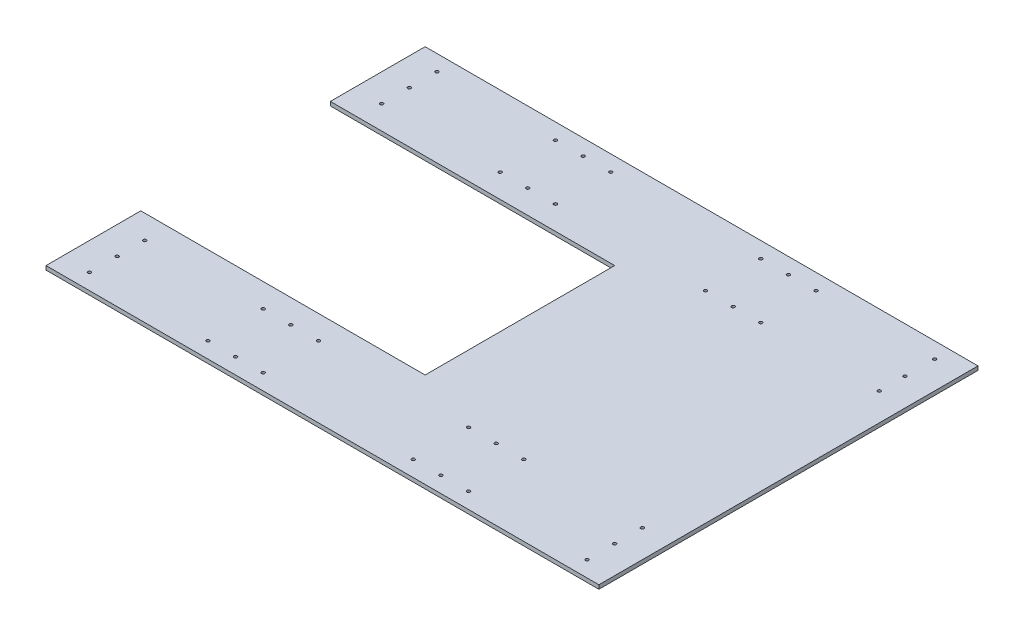
SolidWorks part; units mm, degrees
ref_plane "Front Plane" through (0, 0, 0) normal (0, 0, 1) x (1, 0, 0)
ref_plane "Top Plane" through (0, 0, 0) normal (0, 1, 0) x (1, 0, 0)
ref_plane "Right Plane" through (0, 0, 0) normal (1, 0, 0) x (0, 0, -1)
sketch "Sketch1" plane through (0, 0, 0) normal (0, 1, 0) x (1, 0, 0)
  line L1 (0, 0) -> (889, 0)
  line L2 (0, 0) -> (0, 609.6)
  line L3 (0, 609.6) -> (889, 609.6)
  line L4 (889, 0) -> (889, 609.6)
  dimension "D1" = 609.6
  dimension "D2" = 889
extrude "Boss-Extrude1" add sketch "Sketch1" along normal blind 6.35
sketch "Sketch2" plane through (0, 6.35, 0) normal (0, 1, 0) x (1, 0, 0)
  line L0 (0, 609.6) -> (0, 0) construction
  line L1 (0, 457.2) -> (457.2, 457.2)
  line L2 (0, 457.2) -> (0, 152.4)
  line L3 (0, 152.4) -> (457.2, 152.4)
  line L4 (457.2, 457.2) -> (457.2, 152.4)
  line L5 (889, 609.6) -> (0, 609.6) construction
  line L6 (0, 0) -> (889, 0) construction
  dimension "D1" = 152.4
  dimension "D2" = 152.4
  dimension "D3" = 457.2
  dimension "D4" = 304.8
extrude "Cut-Extrude1" cut sketch "Sketch2" against normal blind 6.35
sketch "Sketch3" plane through (0, 6.35, 0) normal (0, 1, 0) x (1, 0, 0)
  line L0 (0, 609.6) -> (0, 457.2) construction
  line L1 (889, 609.6) -> (0, 609.6) construction
  line L2 (44.45, 756.7858) -> (44.45, -225.0556) construction
  line L3 (-122.3427, 584.2) -> (985.5932, 584.2) construction
  line L4 (457.2, 457.2) -> (0, 457.2) construction
  line L5 (-122.2733, 495.3) -> (985.6237, 495.3) construction
  line L6 (-84.7262, 114.3) -> (1027.24, 114.3) construction
  line L7 (-212.2087, 25.4) -> (1056.8595, 25.4) construction
  line L8 (234.95, 756.7858) -> (234.95, -181.3041) construction
  line L9 (279.4, 771.017) -> (279.4, -225.0556) construction
  line L10 (323.85, 771.017) -> (323.85, -181.3041) construction
  line L11 (565.15, 771.017) -> (565.15, -162.8096) construction
  line L12 (609.6, 801.3225) -> (609.6, -206.7209) construction
  line L13 (654.05, 789.0523) -> (654.05, -204.9626) construction
  line L14 (844.55, 789.0523) -> (844.55, -181.3041) construction
  line L15 (0, 152.4) -> (457.2, 152.4) construction
  line L16 (0, 0) -> (889, 0) construction
  circle A0 centre (44.45, 584.2) radius 2.5527
  circle A1 centre (44.45, 539.75) radius 2.5527
  circle A2 centre (44.45, 495.3) radius 2.5527
  circle A3 centre (44.45, 114.3) radius 2.5527
  circle A4 centre (44.45, 69.85) radius 2.5527
  circle A5 centre (44.45, 25.4) radius 2.5527
  circle A6 centre (234.95, 584.2) radius 2.5527
  circle A7 centre (279.4, 584.2) radius 2.5527
  circle A8 centre (323.85, 584.2) radius 2.5527
  circle A9 centre (234.95, 495.3) radius 2.5527
  circle A10 centre (279.4, 495.3) radius 2.5527
  circle A11 centre (323.85, 495.3) radius 2.5527
  circle A12 centre (234.95, 114.3) radius 2.5527
  circle A13 centre (279.4, 114.3) radius 2.5527
  circle A14 centre (323.85, 114.3) radius 2.5527
  circle A15 centre (234.95, 25.4) radius 2.5527
  circle A16 centre (279.4, 25.4) radius 2.5527
  circle A17 centre (323.85, 25.4) radius 2.5527
  circle A18 centre (565.15, 584.2) radius 2.5527
  circle A19 centre (565.15, 495.3) radius 2.5527
  circle A20 centre (609.6, 584.2) radius 2.5527
  circle A21 centre (609.6, 495.3) radius 2.5527
  circle A22 centre (654.05, 584.2) radius 2.5527
  circle A23 centre (654.05, 495.3) radius 2.5527
  circle A24 centre (565.15, 114.3) radius 2.5527
  circle A25 centre (609.6, 114.3) radius 2.5527
  circle A26 centre (654.05, 114.3) radius 2.5527
  circle A27 centre (565.15, 25.4) radius 2.5527
  circle A28 centre (609.6, 25.4) radius 2.5527
  circle A29 centre (654.05, 25.4) radius 2.5527
  circle A30 centre (844.55, 584.2) radius 2.5527
  circle A31 centre (844.55, 536.575) radius 2.5527
  circle A32 centre (844.55, 495.3) radius 2.5527
  circle A33 centre (844.55, 114.3) radius 2.5527
  circle A34 centre (844.55, 69.85) radius 2.5527
  circle A35 centre (844.55, 25.4) radius 2.5527
  dimension "D1" = 5.1054
  dimension "D2" = 44.45
  dimension "D3" = 25.4
  dimension "D4" = 44.45
  dimension "D5" = 381
  dimension "D6" = 38.1
  dimension "D7" = 88.9
  dimension "D8" = 44.45
  dimension "D9" = 44.45
  dimension "D10" = 47.625
  dimension "D11" = 190.5
  dimension "D12" = 44.45
  dimension "D13" = 38.1
  dimension "D14" = 44.45
  dimension "D15" = 44.45
  dimension "D16" = 241.3
  dimension "D17" = 44.45
  dimension "D18" = 44.45
  dimension "D19" = 190.5
  dimension "D20" = 88.9
  dimension "D21" = 44.45
  dimension "D22" = 41.275
  dimension "D23" = 25.4
extrude "Cut-Extrude2" cut sketch "Sketch3" against normal blind 6.35
